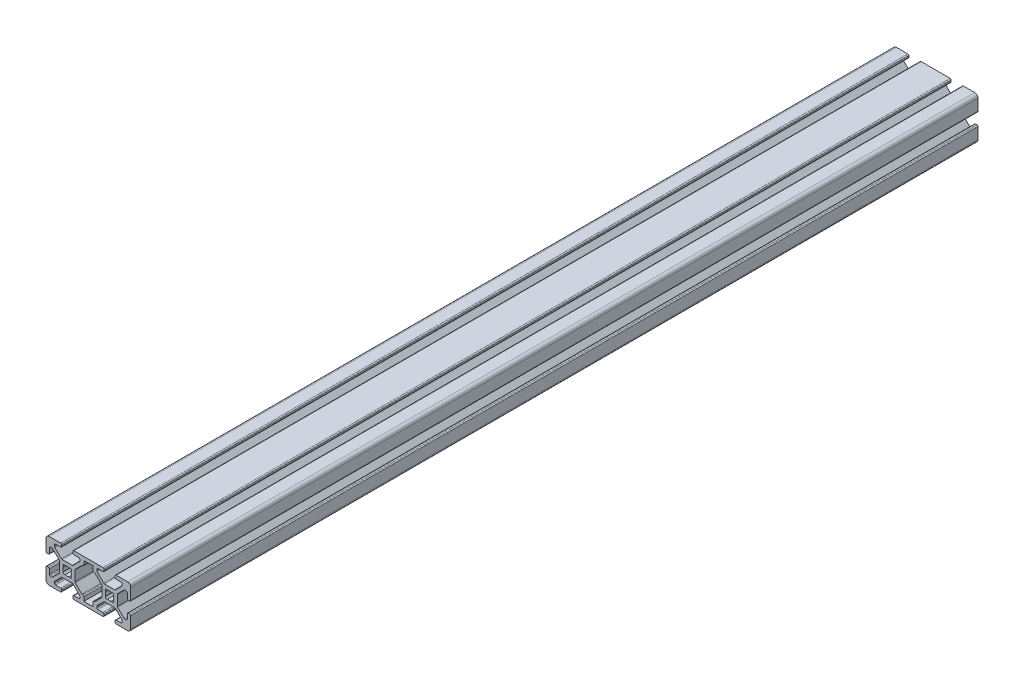
SolidWorks part; units mm, degrees
ref_plane "Front Plane" through (0, 0, 0) normal (0, 0, 1) x (1, 0, 0)
ref_plane "Top Plane" through (0, 0, 0) normal (0, 1, 0) x (1, 0, 0)
ref_plane "Right Plane" through (0, 0, 0) normal (1, 0, 0) x (0, 0, -1)
sketch "Sketch1" plane through (0, 0, 0) normal (0, 0, 1) x (1, 0, 0)
  line L0 (-2.7464, -3.807) -> (-5.848, -6.9086)
  line L1 (-8.5, -10) -> (-3.1319, -10)
  line L2 (-10, -8.5) -> (-10, -3.1319)
  line L3 (-8.5, 10) -> (-3.1319, 10)
  line L4 (7.8581, -6.495) -> (7.8581, -8.36)
  line L5 (7.8581, -8.36) -> (12.1419, -8.36)
  line L6 (-10, 10) -> (-8.36, 8.36) construction
  line L7 (-2.3914, -3.66) -> (2.3914, -3.66)
  line L8 (-3.66, -2.3914) -> (-3.66, 2.3914)
  line L9 (-2.3914, 3.66) -> (2.3914, 3.66)
  line L10 (3.66, -2.3914) -> (3.66, 2.3914)
  line L11 (8.5, -10) -> (3.1319, -10)
  line L12 (-3.1319, -10) -> (-8.5, -10)
  line L13 (-5.4931, -8.36) -> (-3.1319, -8.36)
  line L14 (2.7464, -3.807) -> (5.848, -6.9086)
  line L15 (3.807, -2.7464) -> (6.9086, -5.848)
  line L16 (-5.995, -14.365) -> (5.995, -14.365)
  line L17 (2.63, -9.4981) -> (2.63, -8.8619)
  line L18 (12.1419, -8.36) -> (12.1419, -6.495)
  line L19 (5.995, -7.8581) -> (5.995, -7.2636)
  line L20 (-10, 3.1319) -> (-10, 8.5)
  line L21 (3.1319, 8.36) -> (5.4931, 8.36)
  line L22 (7.2636, -5.995) -> (7.3581, -5.995)
  line L23 (8.5, -10) -> (11.5, -10)
  line L24 (-3.807, -2.7464) -> (-6.9086, -5.848)
  line L25 (-9.4981, -2.63) -> (-8.8619, -2.63)
  line L26 (-7.8581, -5.995) -> (-7.2636, -5.995)
  line L27 (-5.995, -7.2636) -> (-5.995, -7.8581)
  line L28 (-2.63, -8.8619) -> (-2.63, -9.4981)
  line L29 (3.1319, 8.36) -> (5.4931, 8.36)
  line L30 (-5.4931, -8.36) -> (-3.1319, -8.36)
  line L31 (-3.807, 2.7464) -> (-6.9086, 5.848)
  line L32 (-2.7464, 3.807) -> (-5.848, 6.9086)
  line L33 (-2.63, 9.4981) -> (-2.63, 8.8619)
  line L34 (-5.995, 7.8581) -> (-5.995, 7.2636)
  line L35 (-7.2636, 5.995) -> (-7.8581, 5.995)
  line L36 (-8.8619, 2.63) -> (-9.4981, 2.63)
  line L37 (3.1319, 10) -> (8.5, 10)
  line L38 (-8.36, 5.4931) -> (-8.36, 3.1319)
  line L39 (2.7464, 3.807) -> (5.848, 6.9086)
  line L40 (3.807, 2.7464) -> (6.9086, 5.848)
  line L41 (7.8581, 6.495) -> (7.8581, 8.36)
  line L42 (7.3581, 5.995) -> (7.2636, 5.995)
  line L43 (5.995, 7.2636) -> (5.995, 7.8581)
  line L44 (2.63, 8.8619) -> (2.63, 9.4981)
  line L45 (7.8581, 8.36) -> (12.1419, 8.36)
  line L46 (5.4931, 8.36) -> (3.1319, 8.36)
  line L47 (12.1419, 8.36) -> (12.1419, 6.495)
  line L48 (8.5, 10) -> (11.5, 10)
  line L49 (-8.36, 5.4931) -> (-8.36, 3.1319)
  line L50 (5.4931, 8.36) -> (3.1319, 8.36)
  line L51 (-3.1319, 8.36) -> (-5.4931, 8.36)
  line L52 (-3.1319, 8.36) -> (-5.4931, 8.36)
  line L53 (10, 8.36) -> (8.36, 8.36) [skipped]
  line L57 (3.1319, -8.36) -> (5.4931, -8.36)
  line L58 (3.1319, -8.36) -> (5.4931, -8.36)
  line L59 (3.1319, -10) -> (8.5, -10)
  line L60 (-8.36, -3.1319) -> (-8.36, -5.4931)
  line L61 (-8.36, -3.1319) -> (-8.36, -5.4931)
  line L62 (-8.36, 10) -> (-8.36, 8.36) [skipped]
  line L64 (-3.1319, -8.36) -> (-5.4931, -8.36)
  line L65 (-3.1319, -8.36) -> (-5.4931, -8.36)
  line L66 (-8.36, 3.1319) -> (-8.36, 5.4931)
  line L67 (-8.36, 3.1319) -> (-8.36, 5.4931)
  line L68 (-8.36, -5.4931) -> (-8.36, -3.1319)
  line L69 (-5.4931, 8.36) -> (-3.1319, 8.36)
  line L70 (-8.36, -5.4931) -> (-8.36, -3.1319)
  line L71 (5.4931, -8.36) -> (3.1319, -8.36)
  line L72 (-8.8619, -2.63) -> (-9.4981, -2.63)
  line L73 (-7.2636, -5.995) -> (-7.8581, -5.995)
  line L74 (-5.995, -7.8581) -> (-5.995, -7.2636)
  line L75 (-2.63, -9.4981) -> (-2.63, -8.8619)
  line L76 (-2.7464, -3.807) -> (-5.848, -6.9086)
  line L77 (-3.807, -2.7464) -> (-6.9086, -5.848)
  line L78 (-5.4931, 8.36) -> (-3.1319, 8.36)
  line L79 (-10, -3.1319) -> (-10, -8.5)
  line L80 (-2.63, 8.8619) -> (-2.63, 9.4981)
  line L81 (-5.995, 7.2636) -> (-5.995, 7.8581)
  line L82 (-7.8581, 5.995) -> (-7.2636, 5.995)
  line L83 (-9.4981, 2.63) -> (-8.8619, 2.63)
  line L84 (-3.807, 2.7464) -> (-6.9086, 5.848)
  line L85 (-2.7464, 3.807) -> (-5.848, 6.9086)
  line L88 (7.2636, 5.995) -> (7.8581, 5.995)
  line L89 (5.995, 7.8581) -> (5.995, 7.2636)
  line L90 (2.63, 9.4981) -> (2.63, 8.8619)
  line L91 (2.7464, 3.807) -> (5.848, 6.9086)
  line L92 (5.4931, -8.36) -> (3.1319, -8.36)
  line L93 (5.995, -7.2636) -> (5.995, -7.8581)
  line L94 (-3.1319, 10) -> (-8.5, 10)
  line L95 (7.8581, -5.995) -> (7.2636, -5.995)
  line L96 (2.63, -8.8619) -> (2.63, -9.4981)
  line L98 (2.7464, -3.807) -> (5.848, -6.9086)
  line L99 (3.807, -2.7464) -> (6.9086, -5.848)
  line L101 (2.3914, -3.66) -> (-2.3914, -3.66)
  line L102 (-3.66, 2.3914) -> (-3.66, -2.3914)
  line L103 (2.3914, 3.66) -> (-2.3914, 3.66)
  line L104 (3.66, 2.3914) -> (3.66, -2.3914)
  line L105 (-10, 8.5) -> (-10, 3.1319)
  line L106 (8.5, 10) -> (3.1319, 10)
  line L108 (3.807, 2.7464) -> (6.9086, 5.848)
  line L109 (17.2536, -3.807) -> (14.152, -6.9086)
  line L110 (11.5, -10) -> (16.8681, -10)
  line L112 (11.5, 10) -> (16.8681, 10)
  line L113 (30, -8.5) -> (30, -3.1319)
  line L114 (30, 3.1319) -> (30, -3.1319) construction
  line L116 (17.6086, -3.66) -> (22.3914, -3.66)
  line L117 (16.34, -2.3914) -> (16.34, 2.3914)
  line L118 (17.6086, 3.66) -> (22.3914, 3.66)
  line L119 (23.66, -2.3914) -> (23.66, 2.3914)
  line L120 (28.5, -10) -> (23.1319, -10)
  line L121 (16.8681, -10) -> (11.5, -10)
  line L122 (14.5069, -8.36) -> (16.8681, -8.36)
  line L123 (22.7464, -3.807) -> (25.848, -6.9086)
  line L124 (23.807, -2.7464) -> (26.9086, -5.848)
  line L125 (22.63, -9.4981) -> (22.63, -8.8619)
  line L126 (28.8619, -2.63) -> (29.4981, -2.63)
  line L127 (25.995, -7.8581) -> (25.995, -7.2636)
  line L129 (23.1319, 8.36) -> (25.4931, 8.36)
  line L130 (27.2636, -5.995) -> (27.8581, -5.995)
  line L131 (28.36, -5.4931) -> (28.36, -3.1319)
  line L132 (16.193, -2.7464) -> (13.0914, -5.848)
  line L135 (14.005, -7.2636) -> (14.005, -7.8581)
  line L136 (17.37, -8.8619) -> (17.37, -9.4981)
  line L137 (23.1319, 8.36) -> (25.4931, 8.36)
  line L138 (14.5069, -8.36) -> (16.8681, -8.36)
  line L139 (16.193, 2.7464) -> (13.0914, 5.848)
  line L140 (17.2536, 3.807) -> (14.152, 6.9086)
  line L141 (17.37, 9.4981) -> (17.37, 8.8619)
  line L142 (14.005, 7.8581) -> (14.005, 7.2636)
  line L145 (23.1319, 10) -> (28.5, 10)
  line L147 (22.7464, 3.807) -> (25.848, 6.9086)
  line L148 (23.807, 2.7464) -> (26.9086, 5.848)
  line L149 (29.4981, 2.63) -> (28.8619, 2.63)
  line L150 (27.8581, 5.995) -> (27.2636, 5.995)
  line L151 (25.995, 7.2636) -> (25.995, 7.8581)
  line L152 (22.63, 8.8619) -> (22.63, 9.4981)
  line L153 (28.36, -5.4931) -> (28.36, -3.1319)
  line L154 (25.4931, 8.36) -> (23.1319, 8.36)
  line L155 (30, -3.1319) -> (30, -8.5)
  line L156 (28.36, -3.1319) -> (28.36, -5.4931)
  line L158 (25.4931, 8.36) -> (23.1319, 8.36)
  line L159 (16.8681, 8.36) -> (14.5069, 8.36)
  line L160 (16.8681, 8.36) -> (14.5069, 8.36)
  line L161 (30, 3.1319) -> (30, 8.5)
  line L162 (28.36, 3.1319) -> (28.36, 5.4931)
  line L163 (28.36, 3.1319) -> (28.36, 5.4931)
  line L164 (23.1319, -8.36) -> (25.4931, -8.36)
  line L165 (23.1319, -8.36) -> (25.4931, -8.36)
  line L166 (23.1319, -10) -> (28.5, -10)
  line L169 (28.36, -3.1319) -> (28.36, -5.4931)
  line L170 (16.8681, -8.36) -> (14.5069, -8.36)
  line L171 (16.8681, -8.36) -> (14.5069, -8.36)
  line L175 (14.5069, 8.36) -> (16.8681, 8.36)
  line L177 (25.4931, -8.36) -> (23.1319, -8.36)
  line L179 (12.7364, -5.995) -> (12.6419, -5.995)
  line L180 (14.005, -7.8581) -> (14.005, -7.2636)
  line L181 (17.37, -9.4981) -> (17.37, -8.8619)
  line L182 (17.2536, -3.807) -> (14.152, -6.9086)
  line L183 (16.193, -2.7464) -> (13.0914, -5.848)
  line L184 (14.5069, 8.36) -> (16.8681, 8.36)
  line L186 (17.37, 8.8619) -> (17.37, 9.4981)
  line L187 (14.005, 7.2636) -> (14.005, 7.8581)
  line L188 (12.6419, 5.995) -> (12.7364, 5.995)
  line L190 (16.193, 2.7464) -> (13.0914, 5.848)
  line L191 (17.2536, 3.807) -> (14.152, 6.9086)
  line L192 (28.36, 5.4931) -> (28.36, 3.1319)
  line L193 (28.8619, 2.63) -> (29.4981, 2.63)
  line L194 (27.2636, 5.995) -> (27.8581, 5.995)
  line L195 (25.995, 7.8581) -> (25.995, 7.2636)
  line L196 (22.63, 9.4981) -> (22.63, 8.8619)
  line L197 (22.7464, 3.807) -> (25.848, 6.9086)
  line L198 (25.4931, -8.36) -> (23.1319, -8.36)
  line L199 (25.995, -7.2636) -> (25.995, -7.8581)
  line L200 (16.8681, 10) -> (11.5, 10)
  line L201 (27.8581, -5.995) -> (27.2636, -5.995)
  line L202 (22.63, -8.8619) -> (22.63, -9.4981)
  line L203 (29.4981, -2.63) -> (28.8619, -2.63)
  line L204 (22.7464, -3.807) -> (25.848, -6.9086)
  line L205 (23.807, -2.7464) -> (26.9086, -5.848)
  line L206 (28.36, 5.4931) -> (28.36, 3.1319)
  line L207 (22.3914, -3.66) -> (17.6086, -3.66)
  line L208 (16.34, 2.3914) -> (16.34, -2.3914)
  line L209 (22.3914, 3.66) -> (17.6086, 3.66)
  line L210 (23.66, 2.3914) -> (23.66, -2.3914)
  line L212 (28.5, 10) -> (23.1319, 10)
  line L213 (30, 8.5) -> (30, 3.1319)
  line L214 (23.807, 2.7464) -> (26.9086, 5.848)
  line L218 (9.4981, 2.63) -> (8.8619, 2.63) [skipped]
  line L219 (8.36, -5.4931) -> (8.36, -3.1319) [skipped]
  arc A0 (-8.5, -10) -> (-10, -8.5) centre (-8.5, -8.5) cw
  arc A1 (7.3581, 5.995) -> (7.8581, 6.495) centre (7.3581, 6.495) ccw
  arc A2 (7.3581, -5.995) -> (7.8581, -6.495) centre (7.3581, -6.495) cw
  arc A3 (-8.5, 10) -> (-10, 8.5) centre (-8.5, 8.5) ccw
  arc A4 (12.1419, 6.495) -> (12.6419, 5.995) centre (12.6419, 6.495) ccw
  arc A5 (12.1419, -6.495) -> (12.6419, -5.995) centre (12.6419, -6.495) cw
  arc A7 (7.2636, -5.995) -> (6.9086, -5.848) centre (7.2636, -5.4931) cw
  arc A8 (5.995, -7.2636) -> (5.848, -6.9086) centre (5.4931, -7.2636) ccw
  arc A9 (5.995, -7.8581) -> (5.4931, -8.36) centre (5.4931, -7.8581) cw
  arc A10 (3.1319, -10) -> (2.63, -9.4981) centre (3.1319, -9.4981) cw
  arc A11 (2.63, -8.8619) -> (3.1319, -8.36) centre (3.1319, -8.8619) cw
  arc A12 (-3.1319, -10) -> (-2.63, -9.4981) centre (-3.1319, -9.4981) ccw
  arc A13 (-2.63, -8.8619) -> (-3.1319, -8.36) centre (-3.1319, -8.8619) ccw
  arc A14 (-5.4931, -8.36) -> (-5.995, -7.8581) centre (-5.4931, -7.8581) cw
  arc A15 (-5.995, -7.2636) -> (-5.848, -6.9086) centre (-5.4931, -7.2636) cw
  arc A16 (-9.4981, -2.63) -> (-10, -3.1319) centre (-9.4981, -3.1319) ccw
  arc A17 (-8.36, -3.1319) -> (-8.8619, -2.63) centre (-8.8619, -3.1319) ccw
  arc A18 (-7.2636, -5.995) -> (-6.9086, -5.848) centre (-7.2636, -5.4931) ccw
  arc A19 (-7.8581, -5.995) -> (-8.36, -5.4931) centre (-7.8581, -5.4931) cw
  arc A20 (-3.807, -2.7464) -> (-3.66, -2.3914) centre (-4.1619, -2.3914) ccw
  arc A21 (-2.3914, -3.66) -> (-2.7464, -3.807) centre (-2.3914, -4.1619) ccw
  arc A22 (2.7464, -3.807) -> (2.3914, -3.66) centre (2.3914, -4.1619) ccw
  arc A23 (3.807, -2.7464) -> (3.66, -2.3914) centre (4.1619, -2.3914) cw
  arc A26 (5.848, 6.9086) -> (5.995, 7.2636) centre (5.4931, 7.2636) ccw
  arc A27 (7.2636, 5.995) -> (6.9086, 5.848) centre (7.2636, 5.4931) ccw
  arc A29 (5.995, 7.8581) -> (5.4931, 8.36) centre (5.4931, 7.8581) ccw
  arc A30 (3.66, 2.3914) -> (3.807, 2.7464) centre (4.1619, 2.3914) cw
  arc A31 (-3.66, 2.3914) -> (-3.807, 2.7464) centre (-4.1619, 2.3914) ccw
  arc A32 (2.3914, 3.66) -> (2.7464, 3.807) centre (2.3914, 4.1619) ccw
  arc A33 (-2.3914, 3.66) -> (-2.7464, 3.807) centre (-2.3914, 4.1619) cw
  arc A34 (3.1319, 8.36) -> (2.63, 8.8619) centre (3.1319, 8.8619) cw
  arc A35 (2.63, 9.4981) -> (3.1319, 10) centre (3.1319, 9.4981) cw
  arc A36 (-9.4981, 2.63) -> (-10, 3.1319) centre (-9.4981, 3.1319) cw
  arc A37 (-8.8619, 2.63) -> (-8.36, 3.1319) centre (-8.8619, 3.1319) ccw
  arc A38 (-3.1319, 8.36) -> (-2.63, 8.8619) centre (-3.1319, 8.8619) ccw
  arc A39 (-2.63, 9.4981) -> (-3.1319, 10) centre (-3.1319, 9.4981) ccw
  arc A40 (-5.848, 6.9086) -> (-5.995, 7.2636) centre (-5.4931, 7.2636) cw
  arc A41 (-5.4931, 8.36) -> (-5.995, 7.8581) centre (-5.4931, 7.8581) ccw
  arc A42 (-6.9086, 5.848) -> (-7.2636, 5.995) centre (-7.2636, 5.4931) ccw
  arc A43 (-7.8581, 5.995) -> (-8.36, 5.4931) centre (-7.8581, 5.4931) ccw
  arc A44 (-1.7677, 0.9356) -> (-1.7677, -0.9356) centre (0, 0) ccw
  arc A45 (-0.9356, 1.7677) -> (-1.7677, 0.9356) centre (-1.4142, 1.4142) ccw
  arc A46 (1.7677, 0.9356) -> (0.9356, 1.7677) centre (1.4142, 1.4142) ccw
  arc A47 (0.9356, -1.7677) -> (1.7677, -0.9356) centre (1.4142, -1.4142) ccw
  arc A48 (-1.7677, -0.9356) -> (-0.9356, -1.7677) centre (-1.4142, -1.4142) ccw
  arc A49 (-0.9356, -1.7677) -> (0.9356, -1.7677) centre (0, 0) ccw
  arc A50 (1.7677, -0.9356) -> (1.7677, 0.9356) centre (0, 0) ccw
  arc A51 (0.9356, 1.7677) -> (-0.9356, 1.7677) centre (0, 0) ccw
  arc A52 (-2.63, -9.4981) -> (-3.1319, -10) centre (-3.1319, -9.4981) cw
  arc A53 (3.1319, -10) -> (2.63, -9.4981) centre (3.1319, -9.4981) cw
  arc A54 (-8.5, -10) -> (-10, -8.5) centre (-8.5, -8.5) cw
  arc A55 (-1.7677, -0.9356) -> (-1.7677, 0.9356) centre (0, 0) cw
  arc A56 (0.9356, -1.7677) -> (-0.9356, -1.7677) centre (0, 0) cw
  arc A57 (1.7677, 0.9356) -> (1.7677, -0.9356) centre (0, 0) cw
  arc A58 (0.9356, 1.7677) -> (1.7677, 0.9356) centre (1.4142, 1.4142) cw
  arc A59 (-0.9356, -1.7677) -> (-1.7677, -0.9356) centre (-1.4142, -1.4142) cw
  arc A60 (-0.9356, 1.7677) -> (0.9356, 1.7677) centre (0, 0) cw
  arc A61 (-5.995, 7.8581) -> (-5.4931, 8.36) centre (-5.4931, 7.8581) cw
  arc A62 (-5.848, 6.9086) -> (-5.995, 7.2636) centre (-5.4931, 7.2636) cw
  arc A63 (-8.36, 5.4931) -> (-7.8581, 5.995) centre (-7.8581, 5.4931) cw
  arc A64 (-6.9086, 5.848) -> (-7.2636, 5.995) centre (-7.2636, 5.4931) ccw
  arc A65 (-9.4981, 2.63) -> (-10, 3.1319) centre (-9.4981, 3.1319) cw
  arc A66 (-8.36, 3.1319) -> (-8.8619, 2.63) centre (-8.8619, 3.1319) cw
  arc A67 (-2.63, 8.8619) -> (-3.1319, 8.36) centre (-3.1319, 8.8619) cw
  arc A68 (-2.63, 9.4981) -> (-3.1319, 10) centre (-3.1319, 9.4981) ccw
  arc A69 (-9.4981, -2.63) -> (-10, -3.1319) centre (-9.4981, -3.1319) ccw
  arc A70 (-8.36, -3.1319) -> (-8.8619, -2.63) centre (-8.8619, -3.1319) ccw
  arc A71 (-3.66, 2.3914) -> (-3.807, 2.7464) centre (-4.1619, 2.3914) ccw
  arc A72 (-3.66, -2.3914) -> (-3.807, -2.7464) centre (-4.1619, -2.3914) cw
  arc A73 (-2.3914, 3.66) -> (-2.7464, 3.807) centre (-2.3914, 4.1619) cw
  arc A74 (-2.3914, -3.66) -> (-2.7464, -3.807) centre (-2.3914, -4.1619) ccw
  arc A75 (-7.8581, -5.995) -> (-8.36, -5.4931) centre (-7.8581, -5.4931) cw
  arc A76 (-5.4931, -8.36) -> (-5.995, -7.8581) centre (-5.4931, -7.8581) cw
  arc A77 (-5.995, -7.2636) -> (-5.848, -6.9086) centre (-5.4931, -7.2636) cw
  arc A78 (-6.9086, -5.848) -> (-7.2636, -5.995) centre (-7.2636, -5.4931) cw
  arc A79 (-2.63, -8.8619) -> (-3.1319, -8.36) centre (-3.1319, -8.8619) ccw
  arc A80 (2.7464, -3.807) -> (2.3914, -3.66) centre (2.3914, -4.1619) ccw
  arc A81 (3.807, -2.7464) -> (3.66, -2.3914) centre (4.1619, -2.3914) cw
  arc A82 (3.66, 2.3914) -> (3.807, 2.7464) centre (4.1619, 2.3914) cw
  arc A83 (2.7464, 3.807) -> (2.3914, 3.66) centre (2.3914, 4.1619) cw
  arc A84 (5.995, 7.8581) -> (5.4931, 8.36) centre (5.4931, 7.8581) ccw
  arc A85 (5.995, 7.2636) -> (5.848, 6.9086) centre (5.4931, 7.2636) cw
  arc A86 (3.1319, 8.36) -> (2.63, 8.8619) centre (3.1319, 8.8619) cw
  arc A87 (2.63, 9.4981) -> (3.1319, 10) centre (3.1319, 9.4981) cw
  arc A88 (7.2636, 5.995) -> (6.9086, 5.848) centre (7.2636, 5.4931) ccw
  arc A95 (7.2636, -5.995) -> (6.9086, -5.848) centre (7.2636, -5.4931) cw
  arc A96 (5.995, -7.2636) -> (5.848, -6.9086) centre (5.4931, -7.2636) ccw
  arc A97 (5.995, -7.8581) -> (5.4931, -8.36) centre (5.4931, -7.8581) cw
  arc A98 (2.63, -8.8619) -> (3.1319, -8.36) centre (3.1319, -8.8619) cw
  arc A101 (28.5, -10) -> (30, -8.5) centre (28.5, -8.5) ccw
  arc A102 (30, 8.5) -> (28.5, 10) centre (28.5, 8.5) ccw
  arc A104 (30, -3.1319) -> (29.4981, -2.63) centre (29.4981, -3.1319) ccw
  arc A105 (28.8619, -2.63) -> (28.36, -3.1319) centre (28.8619, -3.1319) ccw
  arc A106 (27.8581, -5.995) -> (28.36, -5.4931) centre (27.8581, -5.4931) ccw
  arc A107 (27.2636, -5.995) -> (26.9086, -5.848) centre (27.2636, -5.4931) cw
  arc A108 (25.995, -7.2636) -> (25.848, -6.9086) centre (25.4931, -7.2636) ccw
  arc A109 (25.995, -7.8581) -> (25.4931, -8.36) centre (25.4931, -7.8581) cw
  arc A110 (23.1319, -10) -> (22.63, -9.4981) centre (23.1319, -9.4981) cw
  arc A111 (22.63, -8.8619) -> (23.1319, -8.36) centre (23.1319, -8.8619) cw
  arc A112 (16.8681, -10) -> (17.37, -9.4981) centre (16.8681, -9.4981) ccw
  arc A113 (17.37, -8.8619) -> (16.8681, -8.36) centre (16.8681, -8.8619) ccw
  arc A114 (14.5069, -8.36) -> (14.005, -7.8581) centre (14.5069, -7.8581) cw
  arc A115 (14.005, -7.2636) -> (14.152, -6.9086) centre (14.5069, -7.2636) cw
  arc A118 (12.7364, -5.995) -> (13.0914, -5.848) centre (12.7364, -5.4931) ccw
  arc A120 (16.193, -2.7464) -> (16.34, -2.3914) centre (15.8381, -2.3914) ccw
  arc A121 (17.6086, -3.66) -> (17.2536, -3.807) centre (17.6086, -4.1619) ccw
  arc A122 (22.7464, -3.807) -> (22.3914, -3.66) centre (22.3914, -4.1619) ccw
  arc A123 (23.807, -2.7464) -> (23.66, -2.3914) centre (24.1619, -2.3914) cw
  arc A124 (29.4981, 2.63) -> (30, 3.1319) centre (29.4981, 3.1319) ccw
  arc A125 (28.8619, 2.63) -> (28.36, 3.1319) centre (28.8619, 3.1319) cw
  arc A126 (25.848, 6.9086) -> (25.995, 7.2636) centre (25.4931, 7.2636) ccw
  arc A127 (27.2636, 5.995) -> (26.9086, 5.848) centre (27.2636, 5.4931) ccw
  arc A128 (28.36, 5.4931) -> (27.8581, 5.995) centre (27.8581, 5.4931) ccw
  arc A129 (25.995, 7.8581) -> (25.4931, 8.36) centre (25.4931, 7.8581) ccw
  arc A130 (23.66, 2.3914) -> (23.807, 2.7464) centre (24.1619, 2.3914) cw
  arc A131 (16.34, 2.3914) -> (16.193, 2.7464) centre (15.8381, 2.3914) ccw
  arc A132 (22.3914, 3.66) -> (22.7464, 3.807) centre (22.3914, 4.1619) ccw
  arc A133 (17.6086, 3.66) -> (17.2536, 3.807) centre (17.6086, 4.1619) cw
  arc A134 (23.1319, 8.36) -> (22.63, 8.8619) centre (23.1319, 8.8619) cw
  arc A135 (22.63, 9.4981) -> (23.1319, 10) centre (23.1319, 9.4981) cw
  arc A138 (16.8681, 8.36) -> (17.37, 8.8619) centre (16.8681, 8.8619) ccw
  arc A139 (17.37, 9.4981) -> (16.8681, 10) centre (16.8681, 9.4981) ccw
  arc A140 (14.152, 6.9086) -> (14.005, 7.2636) centre (14.5069, 7.2636) cw
  arc A141 (14.5069, 8.36) -> (14.005, 7.8581) centre (14.5069, 7.8581) ccw
  arc A142 (13.0914, 5.848) -> (12.7364, 5.995) centre (12.7364, 5.4931) ccw
  arc A144 (18.2323, 0.9356) -> (18.2323, -0.9356) centre (20, 0) ccw
  arc A145 (19.0644, 1.7677) -> (18.2323, 0.9356) centre (18.5858, 1.4142) ccw
  arc A146 (21.7677, 0.9356) -> (20.9356, 1.7677) centre (21.4142, 1.4142) ccw
  arc A147 (20.9356, -1.7677) -> (21.7677, -0.9356) centre (21.4142, -1.4142) ccw
  arc A148 (18.2323, -0.9356) -> (19.0644, -1.7677) centre (18.5858, -1.4142) ccw
  arc A149 (19.0644, -1.7677) -> (20.9356, -1.7677) centre (20, 0) ccw
  arc A150 (21.7677, -0.9356) -> (21.7677, 0.9356) centre (20, 0) ccw
  arc A151 (20.9356, 1.7677) -> (19.0644, 1.7677) centre (20, 0) ccw
  arc A152 (17.37, -9.4981) -> (16.8681, -10) centre (16.8681, -9.4981) cw
  arc A153 (23.1319, -10) -> (22.63, -9.4981) centre (23.1319, -9.4981) cw
  arc A155 (18.2323, -0.9356) -> (18.2323, 0.9356) centre (20, 0) cw
  arc A156 (20.9356, -1.7677) -> (19.0644, -1.7677) centre (20, 0) cw
  arc A157 (21.7677, 0.9356) -> (21.7677, -0.9356) centre (20, 0) cw
  arc A158 (20.9356, 1.7677) -> (21.7677, 0.9356) centre (21.4142, 1.4142) cw
  arc A159 (19.0644, -1.7677) -> (18.2323, -0.9356) centre (18.5858, -1.4142) cw
  arc A160 (19.0644, 1.7677) -> (20.9356, 1.7677) centre (20, 0) cw
  arc A161 (14.005, 7.8581) -> (14.5069, 8.36) centre (14.5069, 7.8581) cw
  arc A162 (14.152, 6.9086) -> (14.005, 7.2636) centre (14.5069, 7.2636) cw
  arc A164 (13.0914, 5.848) -> (12.7364, 5.995) centre (12.7364, 5.4931) ccw
  arc A167 (17.37, 8.8619) -> (16.8681, 8.36) centre (16.8681, 8.8619) cw
  arc A168 (17.37, 9.4981) -> (16.8681, 10) centre (16.8681, 9.4981) ccw
  arc A171 (16.34, 2.3914) -> (16.193, 2.7464) centre (15.8381, 2.3914) ccw
  arc A172 (16.34, -2.3914) -> (16.193, -2.7464) centre (15.8381, -2.3914) cw
  arc A173 (17.6086, 3.66) -> (17.2536, 3.807) centre (17.6086, 4.1619) cw
  arc A174 (17.6086, -3.66) -> (17.2536, -3.807) centre (17.6086, -4.1619) ccw
  arc A176 (14.5069, -8.36) -> (14.005, -7.8581) centre (14.5069, -7.8581) cw
  arc A177 (14.005, -7.2636) -> (14.152, -6.9086) centre (14.5069, -7.2636) cw
  arc A178 (13.0914, -5.848) -> (12.7364, -5.995) centre (12.7364, -5.4931) cw
  arc A179 (17.37, -8.8619) -> (16.8681, -8.36) centre (16.8681, -8.8619) ccw
  arc A180 (22.7464, -3.807) -> (22.3914, -3.66) centre (22.3914, -4.1619) ccw
  arc A181 (23.807, -2.7464) -> (23.66, -2.3914) centre (24.1619, -2.3914) cw
  arc A182 (23.66, 2.3914) -> (23.807, 2.7464) centre (24.1619, 2.3914) cw
  arc A183 (22.7464, 3.807) -> (22.3914, 3.66) centre (22.3914, 4.1619) cw
  arc A184 (25.995, 7.8581) -> (25.4931, 8.36) centre (25.4931, 7.8581) ccw
  arc A185 (25.995, 7.2636) -> (25.848, 6.9086) centre (25.4931, 7.2636) cw
  arc A186 (23.1319, 8.36) -> (22.63, 8.8619) centre (23.1319, 8.8619) cw
  arc A187 (22.63, 9.4981) -> (23.1319, 10) centre (23.1319, 9.4981) cw
  arc A188 (27.2636, 5.995) -> (26.9086, 5.848) centre (27.2636, 5.4931) ccw
  arc A189 (28.36, 5.4931) -> (27.8581, 5.995) centre (27.8581, 5.4931) ccw
  arc A190 (28.8619, 2.63) -> (28.36, 3.1319) centre (28.8619, 3.1319) cw
  arc A191 (30, 3.1319) -> (29.4981, 2.63) centre (29.4981, 3.1319) cw
  arc A192 (28.8619, -2.63) -> (28.36, -3.1319) centre (28.8619, -3.1319) ccw
  arc A193 (30, -3.1319) -> (29.4981, -2.63) centre (29.4981, -3.1319) ccw
  arc A194 (27.8581, -5.995) -> (28.36, -5.4931) centre (27.8581, -5.4931) ccw
  arc A195 (27.2636, -5.995) -> (26.9086, -5.848) centre (27.2636, -5.4931) cw
  arc A196 (25.995, -7.2636) -> (25.848, -6.9086) centre (25.4931, -7.2636) ccw
  arc A197 (25.995, -7.8581) -> (25.4931, -8.36) centre (25.4931, -7.8581) cw
  arc A198 (22.63, -8.8619) -> (23.1319, -8.36) centre (23.1319, -8.8619) cw
  arc A199 (30, 8.5) -> (28.5, 10) centre (28.5, 8.5) ccw
  point P0 (0, 0)
  point P5 (0, 0)
  point P9 (-10, -10)
  point P11 (0, -10)
  point P14 (0, -3.66)
  point P23 (3.66, 0)
  point P24 (10, 0)
  point P32 (20, 0)
  point P66 (0, 0)
  point P70 (0, 0)
  point P168 (20, 0)
  point P172 (20, -10)
  point P175 (20, -3.66)
  point P182 (23.66, 0)
  point P183 (30, 0)
  point P223 (20, 0)
  point P226 (20, 0)
  dimension "D2" = 1.5
  dimension "D5" = 0.5
  dimension "D6" = 4
  dimension "D7" = 1.19
  dimension "D9" = 0.5
  dimension "D10" = 0.5019
  dimension "D11" = 4
  dimension "D12" = 1.19
  dimension "D13" = 0.5
  dimension "D1" = 20
  dimension "D3" = 11.99
  dimension "D4" = 4
  dimension "D8" = 4
extrude "Boss-Extrude1" add sketch "Sketch1" along normal blind 400
